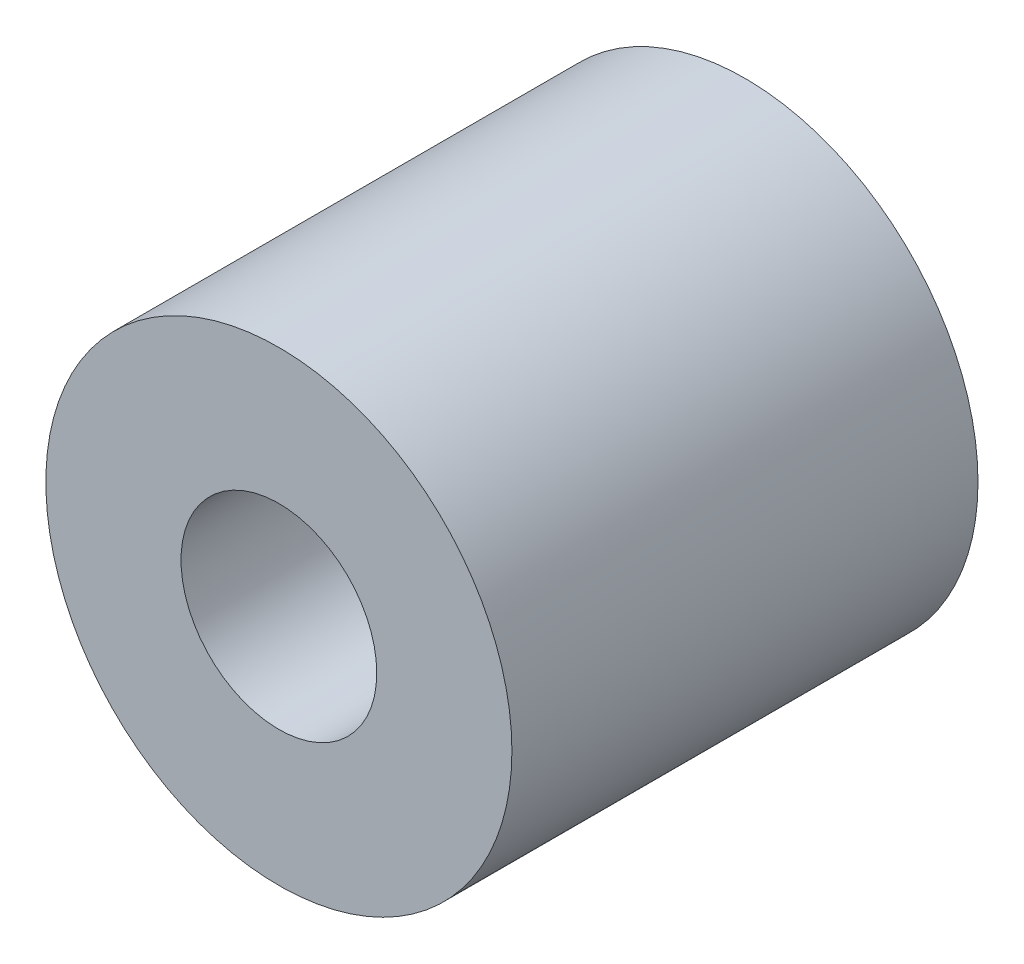
SolidWorks part; units mm, degrees
ref_plane "正面" through (0, 0, 0) normal (0, 0, 1) x (1, 0, 0)
ref_plane "平面" through (0, 0, 0) normal (0, 1, 0) x (1, 0, 0)
ref_plane "右側面" through (0, 0, 0) normal (1, 0, 0) x (0, 0, -1)
sketch "ｽｹｯﾁ1" plane through (0, 0, 0) normal (0, 0, 1) x (1, 0, 0)
  circle A0 centre (0, 0) radius 5
  circle A1 centre (0, 0) radius 2.1
  dimension "D1" = 4.2
  dimension "D2" = 10
extrude "ﾎﾞｽ - 押し出し1" add sketch "ｽｹｯﾁ1" along normal blind 10
